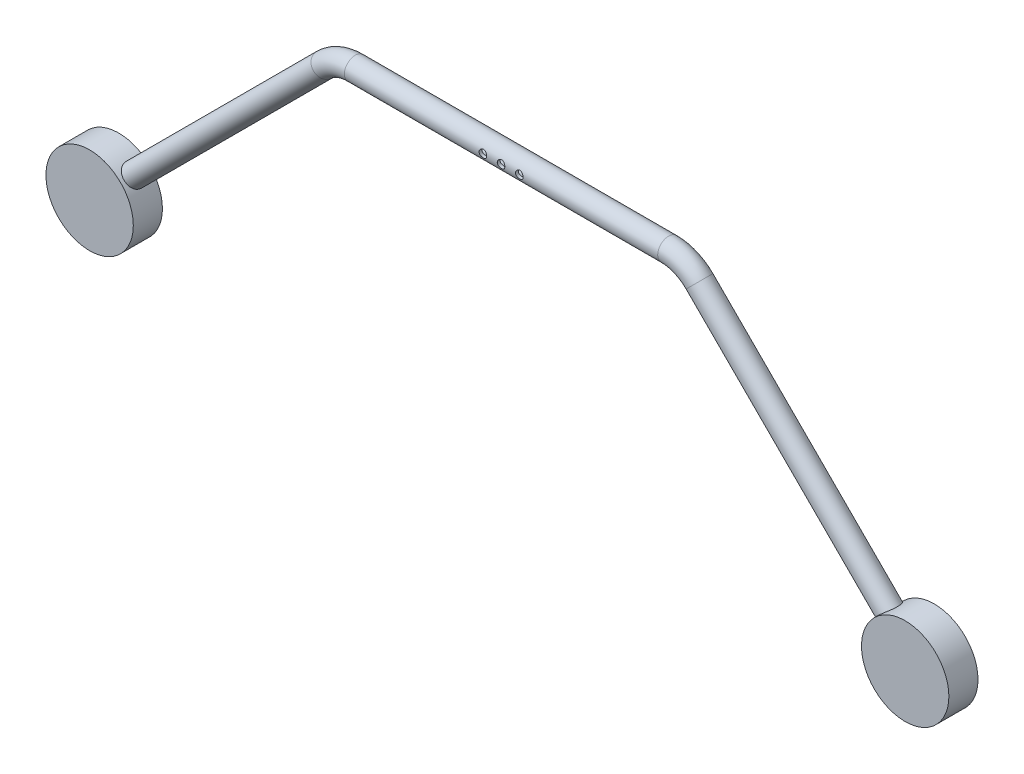
SolidWorks part; units mm, degrees
ref_plane "Front Plane" through (0, 0, 0) normal (0, 0, 1) x (1, 0, 0)
ref_plane "Top Plane" through (0, 0, 0) normal (0, 1, 0) x (1, 0, 0)
ref_plane "Right Plane" through (0, 0, 0) normal (1, 0, 0) x (0, 0, -1)
sketch "Sketch1" plane through (0, 0, 0) normal (0, 0, 1) x (1, 0, 0)
  line L10 (0, 19.4566) -> (0, -8.1997) construction
  line L11 (-355.6, -203.2) -> (-355.6, -165.1) construction
  line L12 (355.6, -203.2) -> (355.6, -165.1) construction
  circle A0 centre (-355.6, -203.2) radius 38.1
  circle A3 centre (-355.6, -203.2) radius 85.471 construction
  circle A4 centre (355.6, -203.2) radius 38.1
  circle A5 centre (355.6, -203.2) radius 85.471 construction
  point P16 (-355.6, -185.2)
  point P17 (355.6, -185.2)
  dimension "D5" = 76.2
  dimension "D6" = 170.942
  dimension "D4" = 18
  dimension "D7" = 18
  dimension "D8" = 711.2
  dimension "D1" = 203.2
extrude "Boss-Extrude1" add sketch "Sketch1" along normal blind 25.4
ref_plane "Plane1" through (0, 0, 12.7) normal (0, 0, 1) x (1, 0, 0)
sketch "Sketch4" plane through (0, 0, 12.7) normal (0, 0, 1) x (1, 0, 0)
  line L0 (-355.6, -203.2) -> (-163.5592, -11.1592)
  line L1 (-136.6185, 0) -> (136.6185, 0)
  line L2 (163.5592, -11.1592) -> (355.6, -203.2)
  arc A0 (136.6185, 0) -> (163.5592, -11.1592) centre (136.6185, -38.1) cw
  arc A1 (-163.5592, -11.1592) -> (-136.6185, 0) centre (-136.6185, -38.1) cw
  dimension "D1" = 38.1
  dimension "D2" = 711.2
  dimension "D3" = 203.2
  dimension "D4" = 135
sweep "Sweep1" add path "Sketch4" circular profile diameter 19.05 parameters "D3"=19.05
sketch "Sketch23" plane through (0, 0, 25.4) normal (0, 0, 1) x (1, 0, 0)
  line L0 (-15.875, 0) -> (15.875, 0) construction
  dimension "D1" = 31.75
shell "Shell1" thickness 2.54
hole_wizard "M6 Clearance Hole1" positions "3DSketch1" profile "Sketch49" hole size "M6" standard "ANSI Metric" end condition through all
sketch3d "3DSketch1"
  point P0 (-15.875, 0, 22.225)
  point P2 (15.875, 0, 22.225)
sketch "Sketch49" plane through (-15.875, 0, 22.225) normal (1, 0, 0) x (0, -1, 0)
  line L0 (0, 0) -> (0, 22.225)
  line L1 (0, 22.225) -> (3.3, 22.225)
  line L2 (3.3, 22.225) -> (3.3, 0.025)
  line L3 (3.3, 0.025) -> (3.325, 0)
  line L5 (3.325, 0) -> (0, 0)
  line L6 (-3.3, 0.025) -> (-3.325, 0) construction
  line L11 (0, -6.35) -> (0, 107.95) construction
  dimension "Thru Hole Dia." = 6.6
  dimension "Thru Hole Depth" = 22.225
  dimension "Near C'Sink Dia." = 6.65
  dimension "Near C'Sink Angle" = 90
hole_wizard "M6 Clearance Hole2" positions "3DSketch2" profile "Sketch51" hole size "M6" standard "ANSI Metric" end condition through all
sketch3d "3DSketch2"
  point P0 (0, 0, 22.225)
sketch "Sketch51" plane through (0, 0, 22.225) normal (1, 0, 0) x (0, -1, 0)
  line L0 (0, 0) -> (0, 22.225)
  line L1 (0, 22.225) -> (3.3, 22.225)
  line L2 (3.3, 22.225) -> (3.3, 0.025)
  line L3 (3.3, 0.025) -> (3.325, 0)
  line L5 (3.325, 0) -> (0, 0)
  line L6 (-3.3, 0.025) -> (-3.325, 0) construction
  line L11 (0, -6.35) -> (0, 107.95) construction
  dimension "Thru Hole Dia." = 6.6
  dimension "Thru Hole Depth" = 22.225
  dimension "Near C'Sink Dia." = 6.65
  dimension "Near C'Sink Angle" = 90
equation "\"Rover_Length\"= 25in"
equation "\"Rover_Width\"= 18in"
equation "\"Rover_Height\"= 12in"
equation "\"Chassis_Wheelbase\"= 28in"
equation "\"Chassis_WheelDiam\"= 171mm"
equation "\"Chassis_ArmDiamWidth\"= 0.75in"
equation "\"Chassis_ArmAngle\"= 135deg"
equation "\"Chassis_HubMountOD\"= 3in"
equation "\"Chassis_WheelBoltHole\"= 36mm"
equation "\"Chassis_WheelBoltNum\"= 4"
equation "\"Chassis_DiffBarLength\"= 12in"
equation "\"Chassis_DiffBarWidth\"= 1in"
equation "\"Chassis_DiffBarHeight\"= 0.5in"
equation "\"Chassis_DiffLinkage_Length\"= 2.5in"
equation "\"D5@Sketch1\"=\"Chassis_HubMountOD\""
equation "\"D4@Sketch1\"=\"Chassis_WheelBoltHole\"/2"
equation "\"D7@Sketch1\"=\"Chassis_WheelBoltHole\"/2"
equation "\"D8@Sketch1\"=\"Chassis_Wheelbase\""
equation "\"D1@Boss-Extrude1\"=\"Chassis_DiffBarWidth\""
equation "\"D2@Sketch4\"=\"Chassis_Wheelbase\""
equation "\"Chassis_ArmHeight\"= 8in"
equation "\"Chassis_MountBracketThickness\"= 0.125in"
equation "\"Chassis_MountBracketWidth\"= 3in"
equation "\"Chassis_MountBacketOverlap\"= 0.5in"
equation "\"Chassis_ArmShaftDiam\"= 0.75in"
equation "\"D3@Sketch4\"=\"Chassis_ArmHeight\""
equation "\"D4@Sketch4\"=\"Chassis_ArmAngle\""
equation "\"D1@Sketch1\"=\"Chassis_ArmHeight\""
equation "\"Chassis_ArmHoleSpacing\" = 1.25in"
equation "\"D1@Sketch23\"=\"Chassis_ArmHoleSpacing\""
